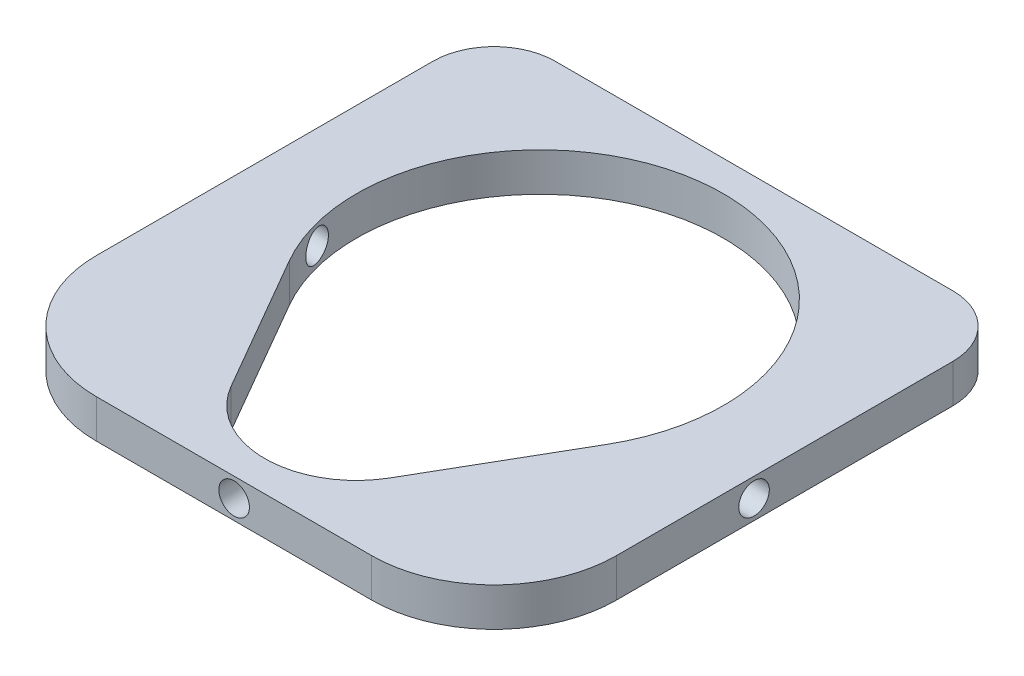
SolidWorks part; units mm, degrees
ref_plane "Front Plane" through (0, 0, 0) normal (0, 0, 1) x (1, 0, 0)
ref_plane "Top Plane" through (0, 0, 0) normal (0, 1, 0) x (1, 0, 0)
ref_plane "Right Plane" through (0, 0, 0) normal (1, 0, 0) x (0, 0, -1)
sketch "Sketch1" plane through (0, 0, 0) normal (0, 1, 0) x (1, 0, 0)
  line L1 (0, 0) -> (85, 0)
  line L2 (0, 0) -> (0, 85)
  line L3 (0, 85) -> (85, 85)
  line L4 (85, 0) -> (85, 85)
  dimension "D1" = 85
  dimension "D2" = 85
extrude "Boss-Extrude1" add sketch "Sketch1" along normal blind 6.3
sketch "Sketch2" plane through (0, 6.3, 0) normal (0, 1, 0) x (1, 0, 0)
  line L0 (0, 85) -> (85, 0) construction
  line L1 (42.5, 85) -> (42.5, 0) construction
  line L2 (85, 85) -> (0, 85) construction
  line L3 (0, 0) -> (85, 0) construction
  line L4 (16.5192, 35) -> (29.5096, 12.5)
  line L5 (55.4904, 12.5) -> (68.4808, 35)
  line L6 (0, 5) -> (85, 5) construction
  line L7 (0, 85) -> (0, 0) construction
  line L8 (85, 0) -> (85, 85) construction
  line L9 (0, 80) -> (85, 80) construction
  arc A0 (68.4808, 35) -> (16.5192, 35) centre (42.5, 50) ccw
  arc A1 (29.5096, 12.5) -> (55.4904, 12.5) centre (42.5, 20) ccw
  dimension "D1" = 30
  dimension "D3" = 15
  dimension "D2" = 30
  dimension "D4" = 5
  dimension "D5" = 5
extrude "Cut-Extrude1" cut sketch "Sketch2" against normal blind 10
sketch "Sketch3" plane through (0, 0, 0) normal (0, 0, 1) x (1, 0, 0)
  line L0 (0, 6.3) -> (85, 0) construction
  circle A0 centre (42.5, 3.15) radius 2.5
  dimension "D1" = 5
extrude "Cut-Extrude2" cut sketch "Sketch3" against normal up to next
sketch "Sketch4" plane through (0, 0, 0) normal (-1, 0, 0) x (0, 0, 1)
  line L0 (-85, 6.3) -> (0, 0) construction
  circle A0 centre (-42.5, 3.15) radius 2.5
  dimension "D1" = 5
extrude "Cut-Extrude3" cut sketch "Sketch4" against normal through all
fillet "Fillet1" radius 20 2 edges at (85, 3.15, 0) (0, 3.15, 0)
fillet "Fillet2" radius 10 2 edges at (85, 3.15, -85) (0, 3.15, -85)
equation "\"D2@Sketch2\"=\"D1@Sketch2\""
equation "\"D3@Sketch2\"=\"D1@Sketch2\"/2"
